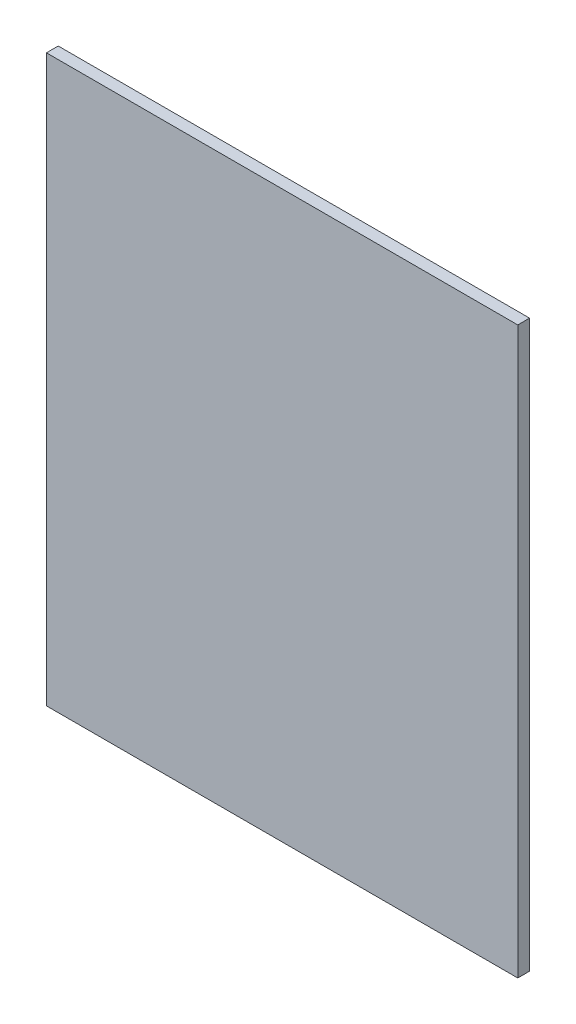
SolidWorks part; units mm, degrees
ref_plane "Front Plane" through (0, 0, 0) normal (0, 0, 1) x (1, 0, 0)
ref_plane "Top Plane" through (0, 0, 0) normal (0, 1, 0) x (1, 0, 0)
ref_plane "Right Plane" through (0, 0, 0) normal (1, 0, 0) x (0, 0, -1)
sketch "Sketch1" plane through (0, 0, 0) normal (0, 0, 1) x (1, 0, 0)
  line L1 (-59.6318, 34.4623) -> (340.3682, 34.4623)
  line L2 (-59.6318, 34.4623) -> (-59.6318, -445.5377)
  line L3 (-59.6318, -445.5377) -> (340.3682, -445.5377)
  line L4 (340.3682, 34.4623) -> (340.3682, -445.5377)
  dimension "D1" = 480
  dimension "D2" = 400
extrude "Extrude1" add sketch "Sketch1" along normal blind 10
